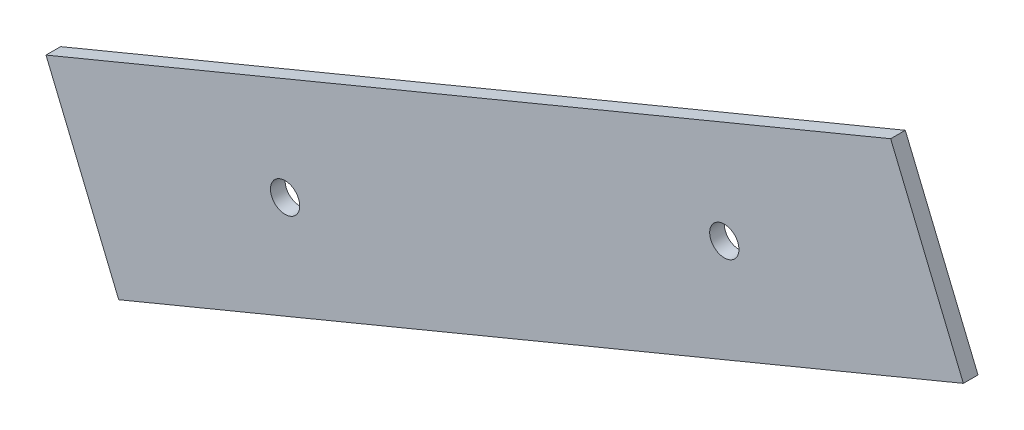
SolidWorks part; units mm, degrees
ref_plane "Front Plane" through (0, 0, 0) normal (0, 0, 1) x (1, 0, 0)
ref_plane "Top Plane" through (0, 0, 0) normal (0, 1, 0) x (1, 0, 0)
ref_plane "Right Plane" through (0, 0, 0) normal (1, 0, 0) x (0, 0, -1)
sketch "Sketch1" plane through (0, 0, 0) normal (0, 0, 1) x (1, 0, 0)
  line L0 (-56.7911, -16.391) -> (-46.8496, -40.3918)
  line L1 (-46.8496, -40.3918) -> (68.6353, 7.4436)
  line L2 (68.6353, 7.4436) -> (58.6938, 31.4445)
  line L3 (-56.7911, -16.391) -> (58.6938, 31.4445)
  line L4 (-51.8204, -28.3914) -> (63.6646, 19.444) construction
  line L5 (0.9513, 7.5267) -> (10.8928, -16.4741) construction
  line L6 (-0.5794, 11.2223) -> (22.5781, -44.6849) construction
  circle A0 centre (-24.104, -16.9109) radius 2
  circle A1 centre (35.9482, 7.9635) radius 2
  point P14 (-0.5794, 11.2223)
  dimension "D2" = 4
  dimension "D1" = 125
extrude "Boss-Extrude1" add sketch "Sketch1" along normal blind 2
